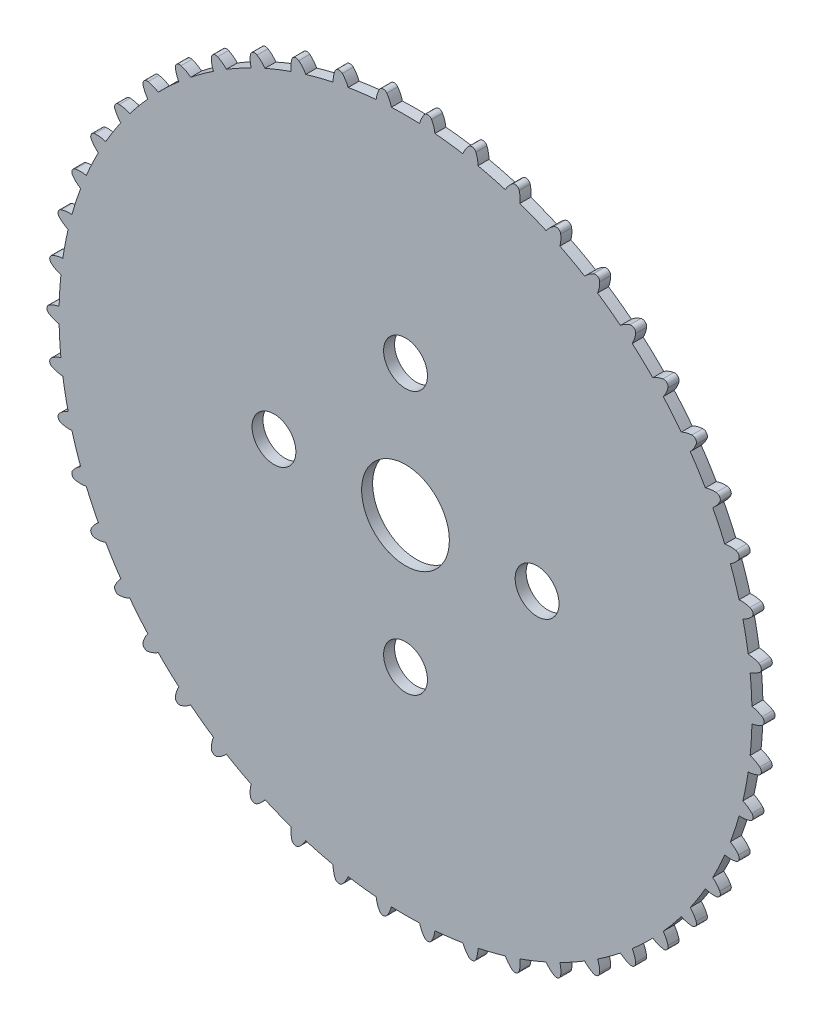
SolidWorks part; units mm, degrees
ref_plane "Front Plane" through (0, 0, 0) normal (0, 0, 1) x (1, 0, 0)
ref_plane "Top Plane" through (0, 0, 0) normal (0, 1, 0) x (1, 0, 0)
ref_plane "Right Plane" through (0, 0, 0) normal (1, 0, 0) x (0, 0, -1)
sketch "Sketch1" plane through (0, 0, 0) normal (0, 0, 1) x (1, 0, 0)
  arc A0 (-31.5924, -0.695) -> (-31.4306, -3.2677) centre (0, 0) ccw
  arc A1 (-32.6902, 4.1297) -> (-31.2558, 4.6515) centre (-31.127, 2.0647) cw
  arc A2 (-32.6902, 4.1297) -> (-31.4306, 3.2677) centre (-30.6625, 5.7411) ccw
  circle A3 centre (0, 0) radius 4
  arc A4 (-31.9148, 8.1943) -> (-30.4263, 8.5322) centre (-30.6227, 5.9496) cw
  arc A9 (-32.521, -0.3384) -> (-31.5923, -0.6974) centre (-31.1403, 1.8528) ccw
  arc A10 (-31.5924, -0.695) -> (-31.606, -0.6949) centre (-31.5924, 0.9785) cw
  arc A11 (-32.521, 0.3384) -> (-31.5923, 0.6974) centre (-31.1403, -1.8528) cw
  arc A12 (-31.9148, 8.1943) -> (-30.7732, 7.1812) centre (-29.7012, 9.5389) ccw
  arc A13 (-30.6361, 12.1297) -> (-29.117, 12.2783) centre (-29.6356, 9.7408) cw
  arc A14 (-30.6361, 12.1297) -> (-29.6305, 10.9815) centre (-28.2714, 13.1862) ccw
  arc A15 (-28.8743, 15.8738) -> (-27.3486, 15.8309) centre (-28.1811, 13.3783) cw
  arc A16 (-28.8743, 15.8738) -> (-28.0205, 14.6086) centre (-26.3958, 16.6256) ccw
  arc A17 (-26.6571, 19.3675) -> (-25.1488, 19.1337) centre (-26.2821, 16.8048) cw
  arc A18 (-26.6571, 19.3675) -> (-25.9686, 18.0053) centre (-24.1039, 19.8028) ccw
  arc A19 (-24.0195, 22.5558) -> (-22.5524, 22.1348) centre (-23.9686, 19.9663) cw
  arc A20 (-24.0195, 22.5558) -> (-23.5072, 21.118) centre (-21.4319, 22.6677) ccw
  arc A21 (-21.0031, 25.3884) -> (-19.6003, 24.7868) centre (-21.2772, 22.813) cw
  arc A22 (-21.0031, 25.3884) -> (-20.6751, 23.8977) centre (-18.4219, 25.175) ccw
  arc A23 (-17.6555, 27.8206) -> (-16.3392, 27.048) centre (-18.2502, 25.2998) cw
  arc A24 (-17.6555, 27.8206) -> (-17.5168, 26.3006) centre (-15.1214, 27.2854) ccw
  arc A25 (-14.0294, 29.8141) -> (-12.8203, 28.8825) centre (-14.9354, 27.3877) cw
  arc A26 (-14.0294, 29.8141) -> (-14.0824, 28.2886) centre (-11.5824, 28.9655) ccw
  arc A27 (-10.1821, 31.3373) -> (-9.0993, 30.2616) centre (-11.385, 29.0436) cw
  arc A28 (-10.1821, 31.3373) -> (-10.4258, 29.8306) centre (-7.8607, 30.1887) ccw
  arc A29 (-6.1742, 32.3664) -> (-5.2348, 31.1634) centre (-7.6551, 30.2415) cw
  arc A30 (-6.1742, 32.3664) -> (-6.6049, 30.902) centre (-4.0151, 30.9359) ccw
  arc A31 (-2.0689, 32.885) -> (-1.2877, 31.5738) centre (-3.8045, 30.9625) cw
  arc A32 (-2.0689, 32.885) -> (-2.6797, 31.4862) centre (-0.1061, 31.1952) ccw
  arc A33 (2.0689, 32.885) -> (2.6797, 31.4862) centre (0.1061, 31.1952) cw
  arc A34 (2.0689, 32.885) -> (1.2877, 31.5738) centre (3.8045, 30.9625) ccw
  arc A35 (6.1742, 32.3664) -> (6.6049, 30.902) centre (4.0151, 30.9359) cw
  arc A36 (6.1742, 32.3664) -> (5.2348, 31.1634) centre (7.6551, 30.2415) ccw
  arc A37 (10.1821, 31.3373) -> (10.4258, 29.8306) centre (7.8607, 30.1887) cw
  arc A38 (10.1821, 31.3373) -> (9.0993, 30.2616) centre (11.385, 29.0436) ccw
  arc A39 (14.0294, 29.8141) -> (14.0824, 28.2886) centre (11.5824, 28.9655) cw
  arc A40 (14.0294, 29.8141) -> (12.8203, 28.8825) centre (14.9354, 27.3877) ccw
  arc A41 (17.6555, 27.8206) -> (17.5168, 26.3006) centre (15.1214, 27.2854) cw
  arc A42 (17.6555, 27.8206) -> (16.3392, 27.048) centre (18.2502, 25.2998) ccw
  arc A43 (21.0031, 25.3884) -> (20.6751, 23.8977) centre (18.4219, 25.175) cw
  arc A44 (21.0031, 25.3884) -> (19.6003, 24.7868) centre (21.2772, 22.813) ccw
  arc A45 (24.0195, 22.5558) -> (23.5072, 21.118) centre (21.4319, 22.6677) cw
  arc A46 (24.0195, 22.5558) -> (22.5524, 22.1348) centre (23.9686, 19.9663) ccw
  arc A47 (26.6571, 19.3675) -> (25.9686, 18.0053) centre (24.1039, 19.8028) cw
  arc A48 (26.6571, 19.3675) -> (25.1488, 19.1337) centre (26.2821, 16.8048) ccw
  arc A49 (28.8743, 15.8738) -> (28.0205, 14.6086) centre (26.3958, 16.6256) cw
  arc A50 (28.8743, 15.8738) -> (27.3486, 15.8309) centre (28.1811, 13.3783) ccw
  arc A51 (30.6361, 12.1297) -> (29.6305, 10.9815) centre (28.2714, 13.1862) cw
  arc A52 (30.6361, 12.1297) -> (29.117, 12.2783) centre (29.6356, 9.7408) ccw
  arc A53 (31.9148, 8.1943) -> (30.7732, 7.1812) centre (29.7012, 9.5389) cw
  arc A54 (31.9148, 8.1943) -> (30.4263, 8.5322) centre (30.6227, 5.9496) ccw
  arc A55 (32.6902, 4.1297) -> (31.4306, 3.2677) centre (30.6625, 5.7411) cw
  arc A56 (32.6902, 4.1297) -> (31.2558, 4.6515) centre (31.127, 2.0647) ccw
  arc A57 (32.95, 0) -> (31.5923, -0.6974) centre (31.1403, 1.8528) cw
  arc A58 (32.95, 0) -> (31.5923, 0.6974) centre (31.1403, -1.8528) ccw
  arc A59 (32.6902, -4.1297) -> (31.2558, -4.6515) centre (31.127, -2.0647) cw
  arc A60 (32.6902, -4.1297) -> (31.4306, -3.2677) centre (30.6625, -5.7411) ccw
  arc A61 (31.9148, -8.1943) -> (30.4263, -8.5322) centre (30.6227, -5.9496) cw
  arc A62 (31.9148, -8.1943) -> (30.7732, -7.1812) centre (29.7012, -9.5389) ccw
  arc A63 (30.6361, -12.1297) -> (29.117, -12.2783) centre (29.6356, -9.7408) cw
  arc A64 (30.6361, -12.1297) -> (29.6305, -10.9815) centre (28.2714, -13.1862) ccw
  arc A65 (28.8743, -15.8738) -> (27.3486, -15.8309) centre (28.1811, -13.3783) cw
  arc A66 (28.8743, -15.8738) -> (28.0205, -14.6086) centre (26.3958, -16.6256) ccw
  arc A67 (26.6571, -19.3675) -> (25.1488, -19.1337) centre (26.2821, -16.8048) cw
  arc A68 (26.6571, -19.3675) -> (25.9686, -18.0053) centre (24.1039, -19.8028) ccw
  arc A69 (24.0195, -22.5558) -> (22.5524, -22.1348) centre (23.9686, -19.9663) cw
  arc A70 (24.0195, -22.5558) -> (23.5072, -21.118) centre (21.4319, -22.6677) ccw
  arc A71 (21.0031, -25.3884) -> (19.6003, -24.7868) centre (21.2772, -22.813) cw
  arc A72 (21.0031, -25.3884) -> (20.6751, -23.8977) centre (18.4219, -25.175) ccw
  arc A73 (17.6555, -27.8206) -> (16.3392, -27.048) centre (18.2502, -25.2998) cw
  arc A74 (17.6555, -27.8206) -> (17.5168, -26.3006) centre (15.1214, -27.2854) ccw
  arc A75 (14.0294, -29.8141) -> (12.8203, -28.8825) centre (14.9354, -27.3877) cw
  arc A76 (14.0294, -29.8141) -> (14.0824, -28.2886) centre (11.5824, -28.9655) ccw
  arc A77 (10.1821, -31.3373) -> (9.0993, -30.2616) centre (11.385, -29.0436) cw
  arc A78 (10.1821, -31.3373) -> (10.4258, -29.8306) centre (7.8607, -30.1887) ccw
  arc A79 (6.1742, -32.3664) -> (5.2348, -31.1634) centre (7.6551, -30.2415) cw
  arc A80 (6.1742, -32.3664) -> (6.6049, -30.902) centre (4.0151, -30.9359) ccw
  arc A81 (2.0689, -32.885) -> (1.2877, -31.5738) centre (3.8045, -30.9625) cw
  arc A82 (2.0689, -32.885) -> (2.6797, -31.4862) centre (0.1061, -31.1952) ccw
  arc A83 (-2.0689, -32.885) -> (-2.6797, -31.4862) centre (-0.1061, -31.1952) cw
  arc A84 (-2.0689, -32.885) -> (-1.2877, -31.5738) centre (-3.8045, -30.9625) ccw
  arc A85 (-6.1742, -32.3664) -> (-6.6049, -30.902) centre (-4.0151, -30.9359) cw
  arc A86 (-6.1742, -32.3664) -> (-5.2348, -31.1634) centre (-7.6551, -30.2415) ccw
  arc A87 (-10.1821, -31.3373) -> (-10.4258, -29.8306) centre (-7.8607, -30.1887) cw
  arc A88 (-10.1821, -31.3373) -> (-9.0993, -30.2616) centre (-11.385, -29.0436) ccw
  arc A89 (-14.0294, -29.8141) -> (-14.0824, -28.2886) centre (-11.5824, -28.9655) cw
  arc A90 (-14.0294, -29.8141) -> (-12.8203, -28.8825) centre (-14.9354, -27.3877) ccw
  arc A91 (-17.6555, -27.8206) -> (-17.5168, -26.3006) centre (-15.1214, -27.2854) cw
  arc A92 (-17.6555, -27.8206) -> (-16.3392, -27.048) centre (-18.2502, -25.2998) ccw
  arc A93 (-21.0031, -25.3884) -> (-20.6751, -23.8977) centre (-18.4219, -25.175) cw
  arc A94 (-21.0031, -25.3884) -> (-19.6003, -24.7868) centre (-21.2772, -22.813) ccw
  arc A95 (-24.0195, -22.5558) -> (-23.5072, -21.118) centre (-21.4319, -22.6677) cw
  arc A96 (-24.0195, -22.5558) -> (-22.5524, -22.1348) centre (-23.9686, -19.9663) ccw
  arc A97 (-26.6571, -19.3675) -> (-25.9686, -18.0053) centre (-24.1039, -19.8028) cw
  arc A98 (-26.6571, -19.3675) -> (-25.1488, -19.1337) centre (-26.2821, -16.8048) ccw
  arc A99 (-28.8743, -15.8738) -> (-28.0205, -14.6086) centre (-26.3958, -16.6256) cw
  arc A100 (-28.8743, -15.8738) -> (-27.3486, -15.8309) centre (-28.1811, -13.3783) ccw
  arc A101 (-30.6361, -12.1297) -> (-29.6305, -10.9815) centre (-28.2714, -13.1862) cw
  arc A102 (-30.6361, -12.1297) -> (-29.117, -12.2783) centre (-29.6356, -9.7408) ccw
  arc A103 (-31.9148, -8.1943) -> (-30.7732, -7.1812) centre (-29.7012, -9.5389) cw
  arc A104 (-31.9148, -8.1943) -> (-30.4263, -8.5322) centre (-30.6227, -5.9496) ccw
  arc A105 (-32.6902, -4.1297) -> (-31.4306, -3.2677) centre (-30.6625, -5.7411) cw
  arc A106 (-32.6902, -4.1297) -> (-31.2558, -4.6515) centre (-31.127, -2.0647) ccw
  arc A107 (-31.2558, -4.6515) -> (-30.7732, -7.1812) centre (0, 0) ccw
  arc A108 (-30.4263, -8.5322) -> (-29.6305, -10.9815) centre (0, 0) ccw
  arc A109 (-29.117, -12.2783) -> (-28.0205, -14.6086) centre (0, 0) ccw
  arc A110 (-27.3486, -15.8309) -> (-25.9686, -18.0053) centre (0, 0) ccw
  arc A111 (-31.4306, 3.2677) -> (-31.5923, 0.6974) centre (0, 0) ccw
  arc A112 (-30.7732, 7.1812) -> (-31.2558, 4.6515) centre (0, 0) ccw
  arc A113 (-29.6305, 10.9815) -> (-30.4263, 8.5322) centre (0, 0) ccw
  arc A114 (22.5524, 22.1348) -> (20.6751, 23.8977) centre (0, 0) ccw
  arc A115 (29.117, 12.2783) -> (28.0205, 14.6086) centre (0, 0) ccw
  arc A116 (27.3486, 15.8309) -> (25.9686, 18.0053) centre (0, 0) ccw
  arc A117 (25.1488, 19.1337) -> (23.5072, 21.118) centre (0, 0) ccw
  arc A118 (19.6003, 24.7868) -> (17.5168, 26.3006) centre (0, 0) ccw
  arc A119 (16.3392, 27.048) -> (14.0824, 28.2886) centre (0, 0) ccw
  arc A120 (12.8203, 28.8825) -> (10.4258, 29.8306) centre (0, 0) ccw
  arc A121 (9.0993, 30.2616) -> (6.6049, 30.902) centre (0, 0) ccw
  arc A122 (20.6751, -23.8977) -> (22.5524, -22.1348) centre (0, 0) ccw
  arc A123 (23.5072, -21.118) -> (25.1488, -19.1337) centre (0, 0) ccw
  arc A124 (25.9686, -18.0053) -> (27.3486, -15.8309) centre (0, 0) ccw
  arc A125 (28.0205, -14.6086) -> (29.117, -12.2783) centre (0, 0) ccw
  arc A126 (17.5168, -26.3006) -> (19.6003, -24.7868) centre (0, 0) ccw
  arc A127 (14.0824, -28.2886) -> (16.3392, -27.048) centre (0, 0) ccw
  arc A128 (10.4258, -29.8306) -> (12.8203, -28.8825) centre (0, 0) ccw
  arc A129 (6.6049, -30.902) -> (9.0993, -30.2616) centre (0, 0) ccw
  arc A130 (2.6797, -31.4862) -> (5.2348, -31.1634) centre (0, 0) ccw
  arc A131 (-1.2877, -31.5738) -> (1.2877, -31.5738) centre (0, 0) ccw
  arc A132 (-5.2348, -31.1634) -> (-2.6797, -31.4862) centre (0, 0) ccw
  arc A133 (-9.0993, -30.2616) -> (-6.6049, -30.902) centre (0, 0) ccw
  arc A134 (-12.8203, -28.8825) -> (-10.4258, -29.8306) centre (0, 0) ccw
  arc A135 (-16.3392, -27.048) -> (-14.0824, -28.2886) centre (0, 0) ccw
  arc A136 (-19.6003, -24.7868) -> (-17.5168, -26.3006) centre (0, 0) ccw
  arc A137 (-22.5524, -22.1348) -> (-20.6751, -23.8977) centre (0, 0) ccw
  arc A138 (-25.1488, -19.1337) -> (-23.5072, -21.118) centre (0, 0) ccw
  arc A139 (31.2558, 4.6515) -> (30.7732, 7.1812) centre (0, 0) ccw
  arc A140 (30.4263, 8.5322) -> (29.6305, 10.9815) centre (0, 0) ccw
  arc A141 (31.5923, 0.6974) -> (31.4306, 3.2677) centre (0, 0) ccw
  arc A142 (31.4306, -3.2677) -> (31.5923, -0.6974) centre (0, 0) ccw
  arc A143 (30.7732, -7.1812) -> (31.2558, -4.6515) centre (0, 0) ccw
  arc A144 (-28.0205, 14.6086) -> (-29.117, 12.2783) centre (0, 0) ccw
  arc A145 (-25.9686, 18.0053) -> (-27.3486, 15.8309) centre (0, 0) ccw
  arc A146 (-23.5072, 21.118) -> (-25.1488, 19.1337) centre (0, 0) ccw
  arc A147 (-20.6751, 23.8977) -> (-22.5524, 22.1348) centre (0, 0) ccw
  arc A148 (-17.5168, 26.3006) -> (-19.6003, 24.7868) centre (0, 0) ccw
  arc A149 (-14.0824, 28.2886) -> (-16.3392, 27.048) centre (0, 0) ccw
  arc A150 (-10.4258, 29.8306) -> (-12.8203, 28.8825) centre (0, 0) ccw
  arc A151 (-6.6049, 30.902) -> (-9.0993, 30.2616) centre (0, 0) ccw
  arc A152 (-2.6797, 31.4862) -> (-5.2348, 31.1634) centre (0, 0) ccw
  arc A153 (1.2877, 31.5738) -> (-1.2877, 31.5738) centre (0, 0) ccw
  arc A154 (5.2348, 31.1634) -> (2.6797, 31.4862) centre (0, 0) ccw
  arc A155 (-32.521, 0.3384) -> (-32.521, -0.3384) centre (-32.3078, 0) ccw
  arc A156 (29.6305, -10.9815) -> (30.4263, -8.5322) centre (0, 0) ccw
  point P4 (-32.95, 0)
  point P267 (0, 0)
  dimension "D1" = 63.2
  dimension "D2" = 50
  dimension "D3" = 0.4
  dimension "D4" = 8
  dimension "D6" = 2.59
extrude "Boss-Extrude1" add sketch "Sketch1" along normal blind 1 contours A36 A154 A33 A34 A153 A31 A32 A152 A29 A30 A151 A27 A28 A150 A25 A26 A149 A23 A24 A148 A21 A22 A147 A19 A20 A146 A17 A18 A145 A15 A16 A144 A13 A14 A113 A4 A12 A112 A1 A2 A111 A11 A9 A10 A0 A105 A106 A107 A103 A104
fillet "Fillet1" radius 0.4 1 edges at (-30.6361, 12.1297, 0.5)
fillet "Fillet2" radius 0.4 33 edges at (21.0031, 25.3884, 0.5) (17.6555, 27.8206, 0.5) (24.0195, 22.5558, 0.5) (26.6571, 19.3675, 0.5) (28.8743, 15.8738, 0.5) (30.6361, 12.1297, 0.5) (31.9148, 8.1943, 0.5) (32.6902, 4.1297, 0.5) (32.95, 0, 0.5) (32.6902, -4.1297, 0.5) (31.9148, -8.1943, 0.5) (28.8743, -15.8738, 0.5) (26.6571, -19.3675, 0.5) (24.0195, -22.5558, 0.5) (21.0031, -25.3884, 0.5) (17.6555, -27.8206, 0.5) (14.0294, -29.8141, 0.5) (10.1821, -31.3373, 0.5) (6.1742, -32.3664, 0.5) (2.0689, -32.885, 0.5) (-2.0689, -32.885, 0.5) (-6.1742, -32.3664, 0.5) (-17.6555, -27.8206, 0.5) (-14.0294, -29.8141, 0.5) (-10.1821, -31.3373, 0.5) (-21.0031, -25.3884, 0.5) (-24.0195, -22.5558, 0.5) (-26.6571, -19.3675, 0.5) (-28.8743, -15.8738, 0.5) (-31.9148, -8.1943, 0.5) (-32.6902, -4.1297, 0.5) (-31.9148, 8.1943, 0.5) (-32.6902, 4.1297, 0.5)
fillet "Fillet3" radius 0.4 15 edges at (-28.8743, 15.8738, 0.5) (-26.6571, 19.3675, 0.5) (-24.0195, 22.5558, 0.5) (-21.0031, 25.3884, 0.5) (-17.6555, 27.8206, 0.5) (-14.0294, 29.8141, 0.5) (-10.1821, 31.3373, 0.5) (-6.1742, 32.3664, 0.5) (-2.0689, 32.885, 0.5) (2.0689, 32.885, 0.5) (6.1742, 32.3664, 0.5) (10.1821, 31.3373, 0.5) (14.0294, 29.8141, 0.5) (30.6361, -12.1297, 0.5) (-30.6361, -12.1297, 0.5)
sketch "Sketch2" plane through (0, 0, 1) normal (0, 0, 1) x (1, 0, 0)
  circle A0 centre (12, 0) radius 2
  circle A1 centre (0, -12) radius 2
  circle A2 centre (-12, 0) radius 2
  circle A3 centre (0, 12) radius 2
  point P10 (0, 0)
  dimension "D1" = 4
  dimension "D3" = 12
  dimension "D2" = 24
  dimension "D4" = 12
  dimension "D5" = 12
extrude "Cut-Extrude1" cut sketch "Sketch2" against normal blind 1
